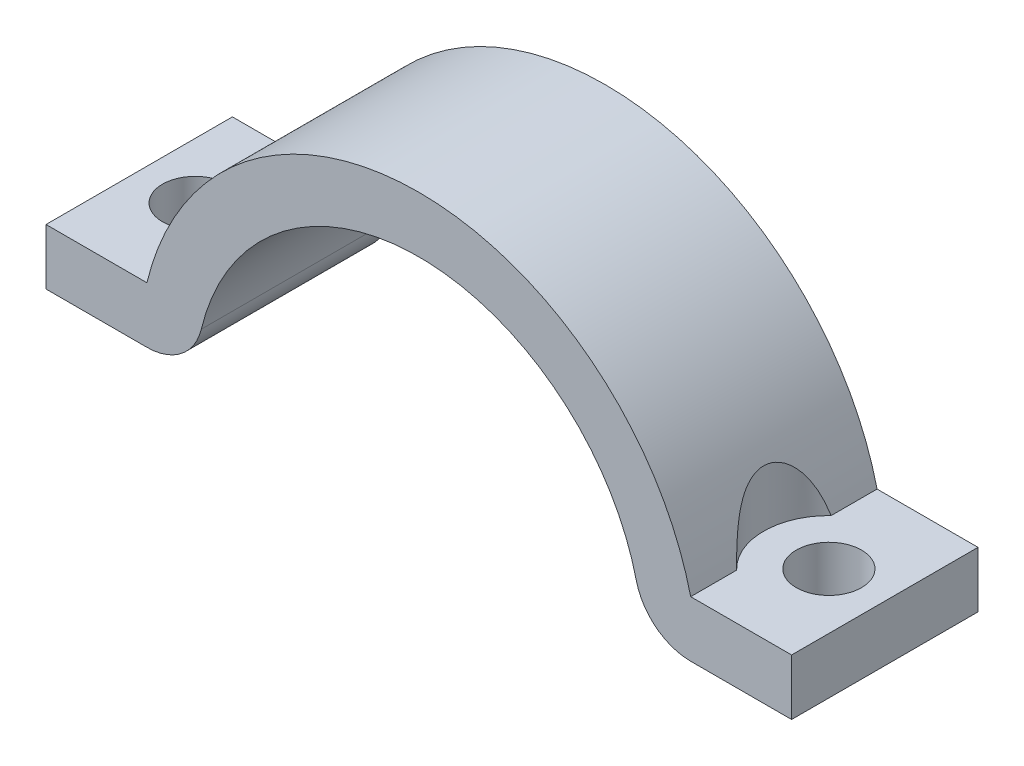
SolidWorks part; units mm, degrees
ref_plane "Plan de face" through (0, 0, 0) normal (0, 0, 1) x (1, 0, 0)
ref_plane "Plan de dessus" through (0, 0, 0) normal (0, 1, 0) x (1, 0, 0)
ref_plane "Plan de droite" through (0, 0, 0) normal (1, 0, 0) x (0, 0, -1)
sketch "Esquisse1" plane through (0, 0, 0) normal (0, 0, 1) x (1, 0, 0)
  line L0 (-14.2536, 0) -> (18.373, 0) construction
  line L1 (-20, 0.5) -> (-14.586, 0.5)
  line L2 (-20, 0.5) -> (-20, 3.5)
  line L3 (-20, 3.5) -> (-14.586, 3.5)
  line L4 (20, 0.5) -> (20, 3.5)
  line L5 (20, 3.5) -> (14.586, 3.5)
  line L6 (14.586, 0.5) -> (20, 0.5)
  arc A0 (14.586, 3.5) -> (-14.586, 3.5) centre (0, 0) ccw
  arc A1 (11.6688, 2.8) -> (-11.6688, 2.8) centre (0, 0) ccw
  arc A2 (14.586, 0.5) -> (11.6688, 2.8) centre (14.586, 3.5) cw
  arc A3 (-11.6688, 2.8) -> (-14.586, 0.5) centre (-14.586, 3.5) cw
  point P11 (0, 0)
  point P13 (0, 0)
  dimension "D1" = 24
  dimension "D2" = 3
  dimension "D7" = 3
  dimension "D3" = 1
  dimension "D4" = 3
  dimension "D5" = 40
  dimension "D6" = 20
extrude "Boss.-Extru.2" add sketch "Esquisse1" along normal blind 10
sketch "Esquisse3" plane through (0, 3.5, 0) normal (0, 1, 0) x (1, 0, 0)
  line L0 (-20, -10) -> (-20, 0) construction
  circle A0 centre (-17, -5) radius 1.75
  circle A1 centre (17, -5) radius 1.75
  point P6 (-20, -5)
  dimension "D1" = 3.5
  dimension "D2" = 34
  dimension "D3" = 17
extrude "Enlèv. mat.-Extru.2" cut sketch "Esquisse3" against normal through all
sketch "Esquisse4" plane through (0, 3.5, 0) normal (0, 1, 0) x (1, 0, 0)
  circle A0 centre (-17, -5) radius 3.5
  circle A1 centre (17, -5) radius 3.5
  dimension "D1" = 7
extrude "Enlèv. mat.-Extru.3" cut sketch "Esquisse4" along normal through all
